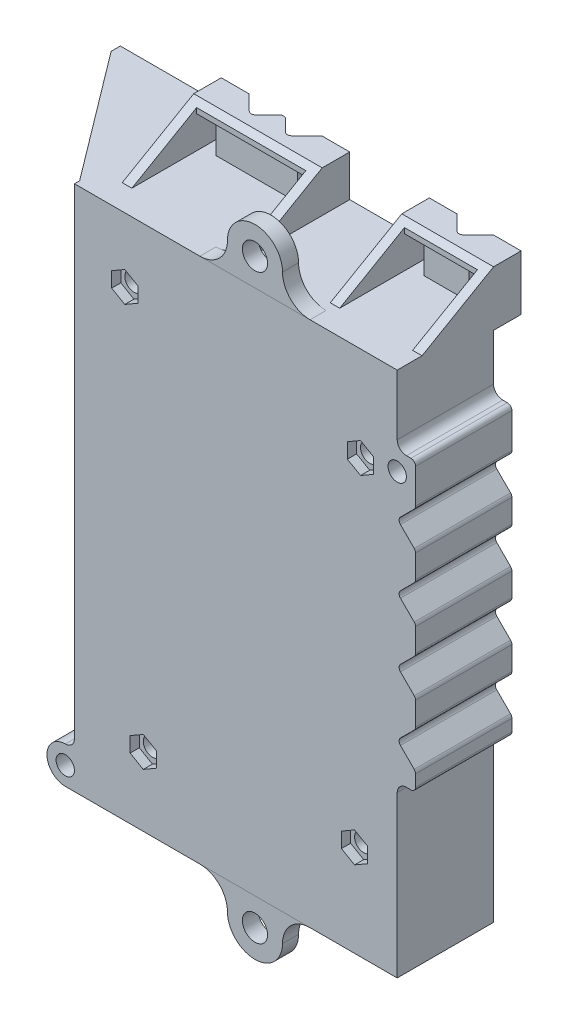
SolidWorks part; units mm, degrees
ref_plane "Front Plane" through (0, 0, 0) normal (0, 0, 1) x (1, 0, 0)
ref_plane "Top Plane" through (0, 0, 0) normal (0, 1, 0) x (1, 0, 0)
ref_plane "Right Plane" through (0, 0, 0) normal (1, 0, 0) x (0, 0, -1)
sketch "Sketch1" plane through (0, 0, 0) normal (0, 0, 1) x (1, 0, 0)
  line L0 (35.175, 42.225) -> (38.175, 42.225)
  line L1 (-35.175, -57.375) -> (34.175, -57.375)
  line L2 (-35.175, -57.375) -> (-35.175, 57.375)
  line L3 (-35.175, 57.375) -> (35.175, 57.375)
  line L4 (35.175, -56.375) -> (35.175, 57.375)
  line L5 (-35.175, -57.375) -> (35.175, 57.375) construction
  line L6 (-35.175, 57.375) -> (35.175, -57.375) construction
  line L7 (39.175, 41.225) -> (39.175, 33.6892)
  line L8 (38.8821, 32.9821) -> (35.8821, 29.9821)
  line L9 (35.8821, 28.5679) -> (38.8821, 25.5679)
  line L10 (39.175, 24.8608) -> (39.175, 19.7892)
  line L11 (38.8821, 19.0821) -> (35.8821, 16.0821)
  line L12 (35.8821, 14.6679) -> (38.8821, 11.6679)
  line L13 (39.175, 10.9608) -> (39.175, 5.8892)
  line L14 (38.8821, 5.1821) -> (35.8821, 2.1821)
  line L15 (35.8821, 0.7679) -> (38.8821, -2.2321)
  line L16 (39.175, -2.9392) -> (39.175, -8.0108)
  line L17 (38.8821, -8.7179) -> (35.8821, -11.7179)
  line L18 (35.8821, -13.1321) -> (38.8821, -16.1321)
  line L19 (39.175, -16.8392) -> (39.175, -19.375)
  line L20 (38.175, -20.375) -> (35.175, -20.375)
  line L21 (35.175, 65.3538) -> (35.175, -80.741) construction
  line L22 (36.5892, 29.275) -> (36.5892, 15.375) construction
  line L23 (36.5892, 15.375) -> (36.5892, 1.475) construction
  line L24 (36.5892, -12.425) -> (36.5892, 1.475) construction
  line L25 (35.175, -56.375) -> (35.175, -57.375)
  line L26 (35.175, -57.375) -> (34.175, -57.375)
  arc A0 (35.8821, 29.9821) -> (35.8821, 28.5679) centre (36.5892, 29.275) ccw
  arc A1 (35.8821, -11.7179) -> (35.8821, -13.1321) centre (36.5892, -12.425) ccw
  arc A2 (35.8821, 2.1821) -> (35.8821, 0.7679) centre (36.5892, 1.475) ccw
  arc A3 (35.8821, 16.0821) -> (35.8821, 14.6679) centre (36.5892, 15.375) ccw
  arc A4 (38.175, 42.225) -> (39.175, 41.225) centre (38.175, 41.225) cw
  arc A5 (38.8821, -16.1321) -> (39.175, -16.8392) centre (38.175, -16.8392) cw
  arc A6 (39.175, -8.0108) -> (38.8821, -8.7179) centre (38.175, -8.0108) cw
  arc A7 (38.8821, -2.2321) -> (39.175, -2.9392) centre (38.175, -2.9392) cw
  arc A8 (39.175, 5.8892) -> (38.8821, 5.1821) centre (38.175, 5.8892) cw
  arc A9 (38.8821, 11.6679) -> (39.175, 10.9608) centre (38.175, 10.9608) cw
  arc A10 (39.175, 19.7892) -> (38.8821, 19.0821) centre (38.175, 19.7892) cw
  arc A11 (38.8821, 25.5679) -> (39.175, 24.8608) centre (38.175, 24.8608) cw
  arc A12 (39.175, 33.6892) -> (38.8821, 32.9821) centre (38.175, 33.6892) cw
  arc A14 (39.175, -19.375) -> (38.175, -20.375) centre (38.175, -19.375) cw
  point P0 (0, 0)
  point P26 (35.175, 29.275)
  point P29 (35.175, -12.425)
  point P32 (35.175, 1.475)
  point P35 (35.175, 15.375)
  dimension "D7" = 1
  dimension "D8" = 1
  dimension "D11" = 1
  dimension "D12" = 1
  dimension "D15" = 1
  dimension "D1" = 114.75
  dimension "D2" = 70.35
  dimension "D3" = 15.15
  dimension "D4" = 4
  dimension "D5" = 0
  dimension "D6" = 135
  dimension "D9" = 12.95
  dimension "D10" = 13.9
  dimension "D14" = 62.6
extrude "Boss-Extrude1" add sketch "Sketch1" along normal blind 21
fillet "Fillet1" radius 2 2 edges at (35.175, -20.375, 10.5) (35.175, 42.225, 10.5)
sketch "Sketch2" plane through (0, 0, 0) normal (0, 0, -1) x (-1, 0, 0)
  line L0 (-35.175, -57.375) -> (-35.175, -22.375) construction
  line L1 (-32.175, -54.375) -> (32.175, -54.375)
  line L2 (-32.175, -54.375) -> (-32.175, 54.375)
  line L3 (-32.175, 54.375) -> (32.175, 54.375)
  line L4 (32.175, -54.375) -> (32.175, 54.375)
  line L5 (-32.175, -54.375) -> (32.175, 54.375) construction
  line L6 (-32.175, 54.375) -> (32.175, -54.375) construction
  line L7 (35.175, -57.375) -> (-35.175, -57.375) construction
  point P0 (0, 0)
  dimension "D1" = 3
  dimension "D2" = 3
extrude "Cut-Extrude1" cut sketch "Sketch2" against normal blind 17.5
sketch "Sketch3" plane through (0, 0, 21) normal (0, 0, 1) x (1, 0, 0)
  line L0 (-35.175, -57.375) -> (-35.175, 57.375) construction
  line L1 (-35.175, 57.375) -> (35.175, 57.375) construction
  line L2 (-7.825, 57.375) -> (16.175, 57.375)
  line L3 (-59.0793, 0) -> (67.7869, 0) construction
  line L4 (-7.825, -57.375) -> (16.175, -57.375)
  arc A0 (10.175, 63.375) -> (-1.825, 63.375) centre (4.175, 63.375) ccw
  arc A1 (-7.825, 57.375) -> (-1.825, 63.375) centre (-7.825, 63.375) ccw
  arc A2 (16.175, 57.375) -> (10.175, 63.375) centre (16.175, 63.375) cw
  circle A3 centre (4.175, 63.375) radius 2.75
  circle A4 centre (4.175, -63.375) radius 2.75
  arc A5 (10.175, -63.375) -> (-1.825, -63.375) centre (4.175, -63.375) cw
  arc A6 (16.175, -57.375) -> (10.175, -63.375) centre (16.175, -63.375) ccw
  arc A7 (-7.825, -57.375) -> (-1.825, -63.375) centre (-7.825, -63.375) cw
  dimension "D1" = 12
  dimension "D3" = 5.5
  dimension "D2" = 39.35
extrude "Boss-Extrude2" add sketch "Sketch3" against normal blind 3.5 separate body
sketch "Sketch4" plane through (0, 0, 0) normal (0, 0, 1) x (1, 0, 0)
  line L0 (-72.3437, 0) -> (77.169, 0) construction
sketch "Sketch5" plane through (0, 0, 21) normal (0, 0, 1) x (1, 0, 0)
  line L0 (-35.175, -57.375) -> (-49.0523, -57.375) construction
  line L1 (-35.175, -57.375) -> (-35.175, 57.375) construction
  line L2 (-35.175, -47.375) -> (-35.175, -57.375)
  line L3 (-35.175, -57.375) -> (-37.175, -57.375)
  arc A0 (-37.175, -49.375) -> (-37.175, -57.375) centre (-37.175, -53.375) ccw
  arc A1 (-35.175, -47.375) -> (-37.175, -49.375) centre (-37.175, -47.375) cw
  dimension "D1" = 8
  dimension "D2" = 2
extrude "Boss-Extrude4" add sketch "Sketch5" against normal blind 21
sketch "Sketch6" plane through (0, 0, 21) normal (0, 0, 1) x (1, 0, 0)
  line L0 (-35.175, -47.375) -> (-35.175, 57.375) construction
  line L1 (-37.175, -57.375) -> (35.175, -57.375) construction
  circle A0 centre (-37.175, -53.375) radius 2
  dimension "D1" = 4
  dimension "D2" = 2
  dimension "D3" = 4
extrude "Cut-Extrude2" cut sketch "Sketch6" against normal through all
sketch "Sketch7" plane through (0, 0, 0) normal (0, 0, -1) x (-1, 0, 0)
  line L0 (-35.175, 57.375) -> (-35.175, 54.375)
  line L1 (-35.175, 44.225) -> (-35.175, 57.375) construction
  line L2 (-35.175, 54.375) -> (32.175, 54.375)
  line L3 (32.175, -54.375) -> (32.175, 54.375) construction
  line L4 (32.175, -54.375) -> (32.175, 54.375) construction
  line L5 (-35.175, 57.375) -> (35.175, 57.375)
  line L6 (35.175, 57.375) -> (35.175, 22.375)
  line L7 (35.175, -47.375) -> (35.175, 57.375) construction
  line L8 (35.175, 22.375) -> (32.175, 22.375)
  line L9 (32.175, 22.375) -> (32.175, 54.375)
  dimension "D1" = 35
  dimension "D2" = 67.35
extrude "Boss-Extrude5" add sketch "Sketch7" along normal blind 10
sketch "Sketch8" plane through (-35.175, 0, 0) normal (-1, 0, 0) x (0, 0, 1)
  line L0 (-44.7056, 25.625) -> (46.5176, 25.625) construction
  line L1 (-10, 22.375) -> (-10, 57.375) construction
  line L2 (21, 57.375) -> (-10, 57.375) construction
  line L3 (0, -47.375) -> (0, 22.375) construction
  line L4 (0, -13.8412) -> (0, 22.375)
  line L5 (0, 22.375) -> (-10, 22.375)
  line L6 (-10, 22.375) -> (-10, 25.625)
  line L7 (8.6892, -82.9289) -> (8.6892, 79.969) construction
  line L8 (21, -47.375) -> (21, 57.375) construction
  line L9 (11, -93.7489) -> (11, 89.3171) construction
  line L10 (-22.4438, 4.625) -> (25.3317, 4.625) construction
  arc A0 (-10, 25.625) -> (0, -13.8412) centre (-10, 4.625) cw
  circle A1 centre (8.6892, -13.2632) radius 2
  circle A2 centre (8.6892, 22.5132) radius 2
  dimension "D3" = 4
  dimension "D2" = 10
  dimension "D1" = 31.75
  dimension "D4" = 2.3108
  dimension "D5" = 0.578
extrude "Cut-Extrude3" cut sketch "Sketch8" against normal blind 10
sketch "Sketch9" plane through (0, 57.375, 0) normal (0, 1, 0) x (1, 0, 0)
  line L0 (-35.175, -19.8679) -> (-56.175, 8)
  line L1 (-35.175, 0) -> (-35.175, -21) construction
  line L2 (-56.175, 8) -> (-56.175, 10)
  line L3 (-56.175, 10) -> (-35.175, 10)
  line L4 (-35.175, -19.8679) -> (-35.175, 10)
  dimension "D1" = 1.1321
  dimension "D2" = 143
  dimension "D3" = 2
extrude "Boss-Extrude6" add sketch "Sketch9" against normal blind 23
ref_plane "Plane1" through (0, 54.375, 0) normal (0, 1, 0) x (1, 0, 0)
sketch "Sketch10" plane through (0, 54.375, 0) normal (0, 1, 0) x (1, 0, 0)
  line L0 (-33.203, 10) -> (-33.203, -17.5)
  line L1 (-33.203, -17.5) -> (-53.9257, 10)
  line L2 (-56.175, 8) -> (-35.175, -19.8679) construction
  line L3 (-56.175, 10) -> (35.175, 10) construction
  line L4 (-53.9257, 10) -> (-33.203, 10)
  dimension "D1" = 3
  dimension "D2" = 27.5
extrude "Cut-Extrude5" cut sketch "Sketch10" against normal blind 17
sketch "Sketch11" plane through (0, 0, -10) normal (0, 0, -1) x (-1, 0, 0)
  line L0 (33.203, 54.375) -> (32.175, 54.375)
  line L1 (32.175, 54.375) -> (32.175, 37.375)
  line L2 (32.175, -54.375) -> (32.175, 54.375) construction
  line L3 (32.175, 37.375) -> (33.203, 37.375)
  line L4 (33.203, 37.375) -> (33.203, 54.375) construction
  line L5 (33.203, 37.375) -> (33.203, 54.375)
  line L6 (33.203, 37.375) -> (33.203, 54.375) construction
  dimension "D1" = 17
extrude "Cut-Extrude6" cut sketch "Sketch11" against normal blind 27.5
sketch "Sketch12" plane through (0, 0, -10) normal (0, 0, -1) x (-1, 0, 0)
  line L0 (32.175, 57.375) -> (-35.175, 57.375)
  line L1 (56.175, 57.375) -> (-35.175, 57.375) construction
  line L2 (-35.175, 57.375) -> (-35.175, 54.375)
  line L3 (-35.175, 54.375) -> (32.175, 54.375)
  line L4 (-35.175, 54.375) -> (53.9257, 54.375) construction
  line L5 (32.175, 54.375) -> (32.175, 57.375)
  line L6 (32.175, 37.375) -> (32.175, 25.625) construction
extrude "Cut-Extrude7" cut sketch "Sketch12" against normal blind 4
sketch "Sketch13" plane through (0, -57.375, 0) normal (0, -1, 0) x (1, 0, 0)
  line L0 (7.475, 0) -> (7.475, 13)
  line L1 (-37.175, 0) -> (35.175, 0) construction
  line L2 (7.475, 13) -> (22.475, 13)
  line L3 (22.475, 13) -> (22.475, 0)
  line L4 (35.175, 21) -> (35.175, 0) construction
  line L5 (22.475, 0) -> (7.475, 0)
  dimension "D1" = 15
  dimension "D2" = 13
  dimension "D3" = 12.7
extrude "Cut-Extrude8" cut sketch "Sketch13" against normal blind 4
sketch "Sketch14" plane through (35.175, 0, 0) normal (1, 0, 0) x (0, 0, -1)
  line L0 (-15.5885, 57.375) -> (0, 66.375)
  line L1 (-21, 57.375) -> (6, 57.375) construction
  line L2 (0, 66.375) -> (6, 66.375)
  line L3 (6, 66.375) -> (6, 57.375)
  line L4 (6, 57.375) -> (-15.5885, 57.375)
  dimension "D1" = 5.4115
  dimension "D2" = 6
  dimension "D3" = 150
extrude "Boss-Extrude7" add sketch "Sketch14" against normal blind 20
sketch "Sketch15" plane through (0, 66.375, 0) normal (0, 1, 0) x (1, 0, 0)
  line L0 (35.175, 6) -> (29.1248, 6)
  line L1 (15.175, 6) -> (35.175, 6) construction
  line L2 (29.1248, 6) -> (25.8821, 2.7574)
  line L3 (24.4679, 2.7574) -> (21.2253, 6)
  line L4 (21.2253, 6) -> (15.175, 6)
  line L5 (25.175, 20.1283) -> (25.175, -19.4875) construction
  line L6 (13.2661, 2.4645) -> (34.0827, 2.4645) construction
  line L7 (15.175, 0) -> (35.175, 0) construction
  line L8 (21.2253, 6) -> (29.1248, 6)
  arc A0 (25.8821, 2.7574) -> (24.4679, 2.7574) centre (25.175, 3.4645) cw
  point P13 (25.175, 2.0503)
  line M4 (35.175, 6) -> (15.175, 6)
  dimension "D2" = 1
  dimension "D1" = 7.8995
  dimension "D3" = 2.4645
extrude "Cut-Extrude9" cut sketch "Sketch15" against normal blind 20 contours A0 L2 L3 M4
sketch "Sketch16" plane through (0, 0, -6) normal (0, 0, -1) x (-1, 0, 0)
  line L0 (-20.2253, 64.375) -> (-20.2253, 57.375)
  line L1 (-20.2253, 57.375) -> (-17.225, 57.375)
  line L2 (-17.225, 57.375) -> (-17.225, 64.375)
  line L3 (-17.225, 64.375) -> (-20.2253, 64.375)
  line L4 (-25.175, 79.2901) -> (-25.175, 42.5315) construction
  line L5 (-30.1248, 57.375) -> (-33.125, 57.375)
  line L6 (-33.125, 57.375) -> (-33.125, 64.375)
  line L7 (-33.125, 64.375) -> (-30.1248, 64.375)
  line L8 (-30.1248, 64.375) -> (-30.1248, 57.375)
  line L9 (-21.2253, 54.375) -> (-21.2253, 66.375) construction
  line L10 (7.825, 57.375) -> (-16.175, 57.375) construction
  line L11 (-15.175, 66.375) -> (-21.2253, 66.375) construction
  line L12 (-35.175, 66.375) -> (-35.175, 54.375) construction
  dimension "D1" = 1
  dimension "D2" = 2
  dimension "D3" = 2.05
extrude "Cut-Extrude10" cut sketch "Sketch16" against normal up to next
sketch "Sketch17" plane through (0, 0, 21) normal (0, 0, 1) x (1, 0, 0)
  line L0 (17.225, 65.5297) -> (33.125, 65.5297)
  line L1 (33.125, 65.5297) -> (33.125, 57.375)
  line L2 (-35.175, 57.375) -> (35.175, 57.375) construction
  line L3 (17.225, 65.5297) -> (17.225, 57.375)
  line L4 (15.175, 57.375) -> (17.225, 57.375) construction
  line L5 (17.225, 64.375) -> (20.2253, 64.375) construction
  line L6 (17.225, 57.375) -> (33.125, 57.375)
  dimension "D1" = 1.1547
extrude "Cut-Extrude11" cut sketch "Sketch17" against normal blind 19.5359
sketch "Sketch18" plane through (0, 0, 1.4641) normal (0, 0, 1) x (1, 0, 0)
  line L0 (30.1248, 57.375) -> (30.1248, 64.375)
  line L1 (30.1248, 64.375) -> (20.2253, 64.375)
  line L2 (20.2253, 64.375) -> (20.2253, 57.375)
  line L3 (20.2253, 57.375) -> (30.1248, 57.375)
extrude "Cut-Extrude12" cut sketch "Sketch18" against normal blind 1.2
sketch "Sketch19" plane through (0, 57.375, 0) normal (0, 1, 0) x (1, 0, 0)
  line L0 (-30.175, 6) -> (-24.075, 6)
  line L1 (-32.175, 6) -> (15.175, 6) construction
  line L2 (-24.075, 6) -> (-20.8321, 2.7571)
  line L3 (-19.4179, 2.7571) -> (-16.8821, 5.2929)
  line L4 (-15.4679, 5.2929) -> (-12.9321, 2.7571)
  line L5 (-11.5179, 2.7571) -> (-8.275, 6)
  line L6 (-8.275, 6) -> (-2.175, 6)
  line L7 (-2.175, 6) -> (-2.175, 0)
  line L8 (-2.175, 0) -> (-30.175, 0)
  line L9 (-30.175, 0) -> (-30.175, 6)
  line L10 (-16.175, 19.5143) -> (-16.175, -8.8162) construction
  line L11 (15.175, 6) -> (15.175, 0) construction
  arc A0 (-16.8821, 5.2929) -> (-15.4679, 5.2929) centre (-16.175, 4.5858) cw
  arc A1 (-12.9321, 2.7571) -> (-11.5179, 2.7571) centre (-12.225, 3.4642) ccw
  arc A2 (-20.8321, 2.7571) -> (-19.4179, 2.7571) centre (-20.125, 3.4642) ccw
  point P17 (-16.175, 6)
  point P20 (-12.225, 2.05)
  point P23 (-20.125, 2.05)
  dimension "D5" = 1
  dimension "D1" = 6
  dimension "D2" = 17.35
  dimension "D3" = 28
  dimension "D4" = 15.8
  dimension "D6" = 90
extrude "Boss-Extrude8" add sketch "Sketch19" along normal blind 9
sketch "Sketch20" plane through (0, 57.375, 0) normal (0, 1, 0) x (1, 0, 0)
  line L0 (-24.075, 6) -> (-8.275, 6)
  line L1 (-8.275, 6) -> (-11.5179, 2.7571)
  line L2 (-12.9321, 2.7571) -> (-15.4679, 5.2929)
  line L3 (-16.8821, 5.2929) -> (-19.4179, 2.7571)
  line L4 (-20.8321, 2.7571) -> (-24.075, 6)
  line L5 (-16.175, 10.1352) -> (-16.175, 0.5868) construction
  line L6 (-20.8321, 2.7571) -> (-24.075, 6) construction
  arc A0 (-15.4679, 5.2929) -> (-16.8821, 5.2929) centre (-16.175, 4.5858) ccw
  arc A1 (-11.5179, 2.7571) -> (-12.9321, 2.7571) centre (-12.225, 3.4642) cw
  arc A2 (-19.4179, 2.7571) -> (-20.8321, 2.7571) centre (-20.125, 3.4642) cw
  point P11 (-16.175, 6)
  point P14 (-12.225, 2.05)
  point P17 (-20.125, 2.05)
  dimension "D1" = 1
extrude "Cut-Extrude13" cut sketch "Sketch20" against normal blind 9
sketch "Sketch23" plane through (-30.175, 0, 0) normal (-1, 0, 0) x (0, 0, 1)
  line L0 (0, 66.375) -> (15.5885, 57.375)
  line L1 (-8, 57.375) -> (19.8679, 57.375) construction
  line L2 (0, 66.375) -> (15.5885, 57.375) construction
  line L3 (15.5885, 57.375) -> (0, 57.375)
  line L4 (15.5885, 57.375) -> (-6, 57.375) construction
  line L5 (0, 57.375) -> (0, 66.375)
extrude "Boss-Extrude9" add sketch "Sketch23" against normal blind 28
sketch "Sketch21" plane through (0, 0, -6) normal (0, 0, -1) x (-1, 0, 0)
  line L0 (28.075, 64.375) -> (28.075, 57.375)
  line L1 (28.075, 57.375) -> (25.075, 57.375)
  line L2 (25.075, 57.375) -> (25.075, 64.375)
  line L3 (25.075, 64.375) -> (28.075, 64.375)
  line L4 (16.175, 76.358) -> (16.175, 45.8866) construction
  line L5 (30.175, 66.375) -> (30.175, 57.375) construction
  line L6 (2.175, 66.375) -> (2.175, 57.375) construction
  line L7 (4.275, 57.375) -> (7.275, 57.375)
  line L8 (4.275, 64.375) -> (4.275, 57.375)
  line L9 (7.275, 64.375) -> (4.275, 64.375)
  line L10 (7.275, 57.375) -> (7.275, 64.375)
  line L11 (2.175, 57.375) -> (-15.175, 57.375) construction
  line L12 (24.075, 66.375) -> (24.075, 54.375) construction
  line L13 (24.075, 66.375) -> (30.175, 66.375) construction
  point P18 (27.125, 66.375)
  dimension "D1" = 1
  dimension "D2" = 2
  dimension "D3" = 2.1
extrude "Cut-Extrude14" cut sketch "Sketch21" against normal up to next
ref_plane "Plane2" through (0, 0, 17.5) normal (0, 0, 1) x (1, 0, 0)
sketch "Sketch24" plane through (0, 0, 17.5) normal (0, 0, 1) x (1, 0, 0)
  line L0 (-28.075, 57.375) -> (-28.075, 65.5297)
  line L1 (-28.075, 65.5297) -> (-4.275, 65.5297)
  line L2 (-4.275, 65.5297) -> (-4.275, 57.375)
  line L3 (-35.175, 57.375) -> (35.175, 57.375) construction
  line L4 (-4.275, 64.375) -> (-4.275, 57.375) construction
  line L5 (-4.275, 57.375) -> (-28.075, 57.375)
  line L6 (-28.075, 64.375) -> (-25.075, 64.375) construction
  dimension "D1" = 1.1547
extrude "Cut-Extrude15" cut sketch "Sketch24" against normal blind 16.0359
sketch "Sketch25" plane through (0, 0, 1.4641) normal (0, 0, 1) x (1, 0, 0)
  line L0 (-25.075, 57.375) -> (-25.075, 64.375)
  line L1 (-25.075, 64.375) -> (-7.275, 64.375)
  line L2 (-7.275, 64.375) -> (-7.275, 57.375)
  line L3 (-7.275, 57.375) -> (-25.075, 57.375)
extrude "Cut-Extrude16" cut sketch "Sketch25" against normal blind 1.2
sketch "Sketch26" plane through (0, 0, 17.5) normal (0, 0, -1) x (-1, 0, 0)
  line L0 (-21.675, 31.875) -> (-21.675, -26.875) construction
  line L1 (-19.175, 31.875) -> (-19.175, -26.875)
  line L2 (-24.175, 31.875) -> (-24.175, -26.875)
  line L3 (14.5413, 31.875) -> (14.5414, -26.875) construction
  line L4 (17.0413, 31.875) -> (17.0414, -26.875)
  line L5 (12.0413, 31.875) -> (12.0413, -26.875)
  line L6 (-51.9032, 34.375) -> (26.7315, 34.375) construction
  line L7 (-51.0981, -29.375) -> (27.5365, -29.375) construction
  line L8 (33.203, 54.375) -> (-32.175, 54.375) construction
  line L10 (-32.175, 54.375) -> (-32.175, -54.375) construction
  arc A0 (-19.175, 31.875) -> (-24.175, 31.875) centre (-21.675, 31.875) ccw
  arc A1 (-24.175, -26.875) -> (-19.175, -26.875) centre (-21.675, -26.875) ccw
  arc A2 (17.0413, 31.875) -> (12.0413, 31.875) centre (14.5413, 31.875) ccw
  arc A3 (12.0413, -26.875) -> (17.0414, -26.875) centre (14.5414, -26.875) ccw
  point P2 (-21.675, 2.5)
  point P9 (14.5413, 2.5)
  dimension "D5" = 20
  dimension "D1" = 5
  dimension "D2" = 58.75
  dimension "D3" = 5
  dimension "D4" = 58.75
  dimension "D6" = 8
  dimension "D7" = 31.2163
extrude "Boss-Extrude10" add sketch "Sketch26" along normal blind 3.5
sketch "Sketch27" plane through (0, 0, 17.5) normal (0, 0, -1) x (-1, 0, 0)
  line L0 (33.203, 37.375) -> (33.203, 54.375) construction
  line L1 (-27.175, 40.775) -> (-32.175, 40.775)
  line L2 (35.175, 57.375) -> (-35.175, 57.375) construction
  line L3 (32.175, -54.375) -> (32.175, 37.375) construction
  line L4 (21.6049, 41.875) -> (24.203, 40.375)
  line L5 (24.203, 40.375) -> (26.801, 41.875)
  line L6 (26.801, 41.875) -> (26.801, 44.875)
  line L7 (26.801, 44.875) -> (24.203, 46.375)
  line L8 (24.203, 46.375) -> (21.6049, 44.875)
  line L9 (21.6049, 44.875) -> (21.6049, 41.875)
  line L10 (-29.7731, 35.275) -> (-27.175, 33.775)
  line L11 (-27.175, 33.775) -> (-24.5769, 35.275)
  line L12 (-24.5769, 35.275) -> (-24.5769, 38.275)
  line L13 (-24.5769, 38.275) -> (-27.175, 39.775)
  line L14 (-27.175, 39.775) -> (-29.7731, 38.275)
  line L15 (-29.7731, 38.275) -> (-29.7731, 35.275)
  line L16 (-28.4731, -38.875) -> (-25.875, -40.375)
  line L17 (-25.875, -40.375) -> (-23.2769, -38.875)
  line L18 (-23.2769, -38.875) -> (-23.2769, -35.875)
  line L19 (-23.2769, -35.875) -> (-25.875, -34.375)
  line L20 (-25.875, -34.375) -> (-28.4731, -35.875)
  line L21 (-28.4731, -35.875) -> (-28.4731, -38.875)
  line L22 (17.5769, -43.875) -> (20.175, -45.375)
  line L23 (20.175, -45.375) -> (22.7731, -43.875)
  line L24 (22.7731, -43.875) -> (22.7731, -40.875)
  line L25 (22.7731, -40.875) -> (20.175, -39.375)
  line L26 (20.175, -39.375) -> (17.5769, -40.875)
  line L27 (17.5769, -40.875) -> (17.5769, -43.875)
  line L28 (-32.175, -54.375) -> (32.175, -54.375) construction
  line L30 (-32.175, 54.375) -> (-32.175, -54.375) construction
  line L31 (-35.175, -22.375) -> (-35.175, -57.375) construction
  line L32 (-27.175, 32.775) -> (-32.175, 32.775)
  line L33 (-32.175, 54.375) -> (-32.175, -54.375) construction
  line L34 (-25.875, -33.375) -> (-32.175, -33.375)
  line L35 (-35.175, 57.375) -> (-35.175, 44.225) construction
  line L36 (-39.175, 41.225) -> (-39.175, 33.6892) construction
  line L37 (-25.875, -41.375) -> (-32.175, -41.375)
  circle A0 centre (20.175, -42.375) radius 4
  circle A1 centre (20.175, -42.375) radius 2
  circle A2 centre (-25.875, -37.375) radius 4
  circle A3 centre (-25.875, -37.375) radius 2
  circle A4 centre (24.203, 43.375) radius 2
  circle A5 centre (24.203, 43.375) radius 4
  circle A6 centre (-27.175, 36.775) radius 2
  circle A7 centre (-27.175, 36.775) radius 4
  circle A8 centre (24.203, 43.375) radius 2.5981 construction
  circle A9 centre (-27.175, 36.775) radius 2.5981 construction
  circle A10 centre (-25.875, -37.375) radius 2.5981 construction
  circle A11 centre (20.175, -42.375) radius 2.5981 construction
  circle A12 centre (-37.175, 38.225) radius 2
  dimension "D1" = 4
  dimension "D2" = 8
  dimension "D3" = 4
  dimension "D4" = 8
  dimension "D5" = 4
  dimension "D6" = 8
  dimension "D7" = 4
  dimension "D8" = 8
  dimension "D9" = 9
  dimension "D10" = 14
  dimension "D11" = 12
  dimension "D17" = 20.6
  dimension "D18" = 3
  dimension "D21" = 4
  dimension "D12" = 12
  dimension "D13" = 3
  dimension "D14" = 17
  dimension "D15" = 3
  dimension "D16" = 9.3
  dimension "D19" = 8
  dimension "D20" = 3
  dimension "D22" = 2
  dimension "D23" = 6
extrude "Cut-Extrude20" cut sketch "Sketch27" against normal through all contours A6 | A4 | A1 | A3 | A12
sketch "Sketch32" plane through (0, 0, 21) normal (0, 0, 1) x (1, 0, 0)
  line L1 (-21.3451, 41.725) -> (-21.3451, 45.025)
  line L2 (-21.3451, 45.025) -> (-24.203, 46.675)
  line L3 (-24.203, 46.675) -> (-27.0608, 45.025)
  line L4 (-27.0608, 45.025) -> (-27.0608, 41.725)
  line L5 (-27.0608, 41.725) -> (-24.203, 40.075)
  line L6 (-24.203, 40.075) -> (-21.3451, 41.725)
  line L7 (30.0329, 35.125) -> (30.0329, 38.425)
  line L8 (30.0329, 38.425) -> (27.175, 40.075)
  line L9 (27.175, 40.075) -> (24.3171, 38.425)
  line L10 (24.3171, 38.425) -> (24.3171, 35.125)
  line L11 (24.3171, 35.125) -> (27.175, 33.475)
  line L12 (27.175, 33.475) -> (30.0329, 35.125)
  line L13 (-17.3171, -44.025) -> (-17.3171, -40.725)
  line L14 (-17.3171, -40.725) -> (-20.175, -39.075)
  line L15 (-20.175, -39.075) -> (-23.0329, -40.725)
  line L16 (-23.0329, -40.725) -> (-23.0329, -44.025)
  line L17 (-23.0329, -44.025) -> (-20.175, -45.675)
  line L18 (-20.175, -45.675) -> (-17.3171, -44.025)
  line L19 (28.7329, -39.025) -> (28.7329, -35.725)
  line L20 (28.7329, -35.725) -> (25.875, -34.075)
  line L21 (25.875, -34.075) -> (23.0171, -35.725)
  line L22 (23.0171, -35.725) -> (23.0171, -39.025)
  line L23 (23.0171, -39.025) -> (25.875, -40.675)
  line L24 (25.875, -40.675) -> (28.7329, -39.025)
  circle A0 centre (-24.203, 43.375) radius 2.8579 construction
  circle A1 centre (27.175, 36.775) radius 2.8579 construction
  circle A2 centre (-20.175, -42.375) radius 2.8579 construction
  circle A3 centre (25.875, -37.375) radius 2.8579 construction
  dimension "D1" = 3.3
  dimension "D2" = 3.3
  dimension "D3" = 3.3
extrude "Cut-Extrude21" cut sketch "Sketch32" against normal blind 2
sketch "Sketch34" plane through (0, 0, 17.5) normal (0, 0, -1) x (-1, 0, 0)
  line L0 (-27.175, 40.775) -> (-32.175, 40.775)
  line L1 (-32.175, 54.375) -> (-32.175, -54.375) construction
  line L2 (-27.175, 32.775) -> (-32.175, 32.775)
  line L3 (-25.875, -33.375) -> (-32.175, -33.375)
  line L4 (-32.175, 54.375) -> (-32.175, -54.375) construction
  line L5 (-25.875, -41.375) -> (-32.175, -41.375)
  line L6 (32.175, -54.375) -> (32.175, 37.375) construction
  circle A0 centre (24.1122, 43.3921) radius 4
  circle A1 centre (20.175, -42.375) radius 4
  circle A2 centre (-25.875, -37.375) radius 4
  circle A3 centre (-27.175, 36.775) radius 4
  circle M1 centre (-25.875, -37.375) radius 2
  circle M2 centre (20.175, -42.375) radius 2
  circle M3 centre (24.203, 43.375) radius 2
  circle M4 centre (-27.175, 36.775) radius 2
  line M13 (-32.175, 54.375) -> (-32.175, -54.375)
  dimension "D1" = 8
  dimension "D2" = 8
  dimension "D3" = 8
  dimension "D4" = 8
  dimension "D5" = 8.0628
  dimension "D6" = 97.7671
extrude "Boss-Extrude12" add sketch "Sketch34" along normal blind 2 contours A3 M4 | A3 L0 L2 M13 | A0 M3 | A1 M2 | A2 L3 L5 M13 | A2 M1
fillet "Fillet3" radius 4 4 edges at (32.175, 32.775, 16.5) (32.175, 40.775, 16.5) (32.175, -41.375, 16.5) (32.175, -33.375, 16.5)
sketch "Sketch35" plane through (0, 0, 0) normal (0, 0, -1) x (-1, 0, 0)
  line L0 (-39.175, 41.225) -> (-39.175, 33.6892) construction
  circle A0 centre (-35.175, 38.225) radius 2
  dimension "D1" = 4
  dimension "D2" = 6
  dimension "D3" = 4
extrude "Cut-Extrude22" cut sketch "Sketch35" against normal through all
sketch "Sketch36" plane through (-32.175, 0, 0) normal (1, 0, 0) x (0, 0, -1)
  line L0 (-17.5, 27.4964) -> (-17.5, 15.4964)
  line L1 (-17.5, 15.4964) -> (-7.967, 15.4964)
  line L2 (-17.5, 27.4964) -> (-4.5, 27.4964)
  line L3 (-4.5, 27.4964) -> (-4.5, 19.8155)
  line L4 (-17.5, -54.375) -> (-17.5, 37.375) construction
  arc A0 (10, 25.625) -> (0, -13.8412) centre (10, 4.625) ccw construction
  arc A1 (-7.967, 15.4964) -> (-4.5, 19.8155) centre (10, 4.625) cw
  dimension "D1" = 12
  dimension "D2" = 13
  dimension "D3" = 9.533
extrude "Boss-Extrude13" add sketch "Sketch36" along normal blind 4
sketch "Sketch37" plane through (-35.175, 0, 0) normal (-1, 0, 0) x (0, 0, 1)
  line L0 (45.6874, 4.625) -> (-74.0143, 4.625) construction
  line L1 (11, 31.747) -> (11, -10.4344) construction
  arc A1 (0, -13.8412) -> (-10, 25.625) centre (-10, 4.625) ccw construction
  point P7 (11, 4.625)
ref_plane "Plane3" through (0, 4.625, 0) normal (0, -1, 0) x (-1, 0, 0)
mirror "Mirror1" about plane through (0, 4.625, 0) normal (0, -1, 0) of "Boss-Extrude13"
sketch "Sketch38" plane through (-35.175, 0, 0) normal (-1, 0, 0) x (0, 0, 1)
  circle A0 centre (8.6892, -13.2632) radius 2
  circle A1 centre (8.6892, 22.5132) radius 2
  dimension "D1" = 4
  dimension "D2" = 4
extrude "Cut-Extrude23" cut sketch "Sketch38" against normal up to next
sketch "Sketch39" plane through (-28.175, 0, 0) normal (1, 0, 0) x (0, 0, -1)
  line L0 (-4.5, 19.8155) -> (-4.5, 27.4964) construction
  line L1 (-5.8392, 24.1586) -> (-8.6892, 25.8041)
  line L2 (-8.6892, 25.8041) -> (-11.5392, 24.1586)
  line L3 (-11.5392, 24.1586) -> (-11.5392, 20.8677)
  line L4 (-11.5392, 20.8677) -> (-8.6892, 19.2223)
  line L5 (-8.6892, 19.2223) -> (-5.8392, 20.8677)
  line L6 (-5.8392, 20.8677) -> (-5.8392, 24.1586)
  circle A0 centre (-8.6892, 22.5132) radius 2.85 construction
  dimension "D1" = 3.2909
extrude "Cut-Extrude24" cut sketch "Sketch39" against normal blind 3
mirror "Mirror2" about plane through (0, 4.625, 0) normal (0, -1, 0) of "Cut-Extrude24"
